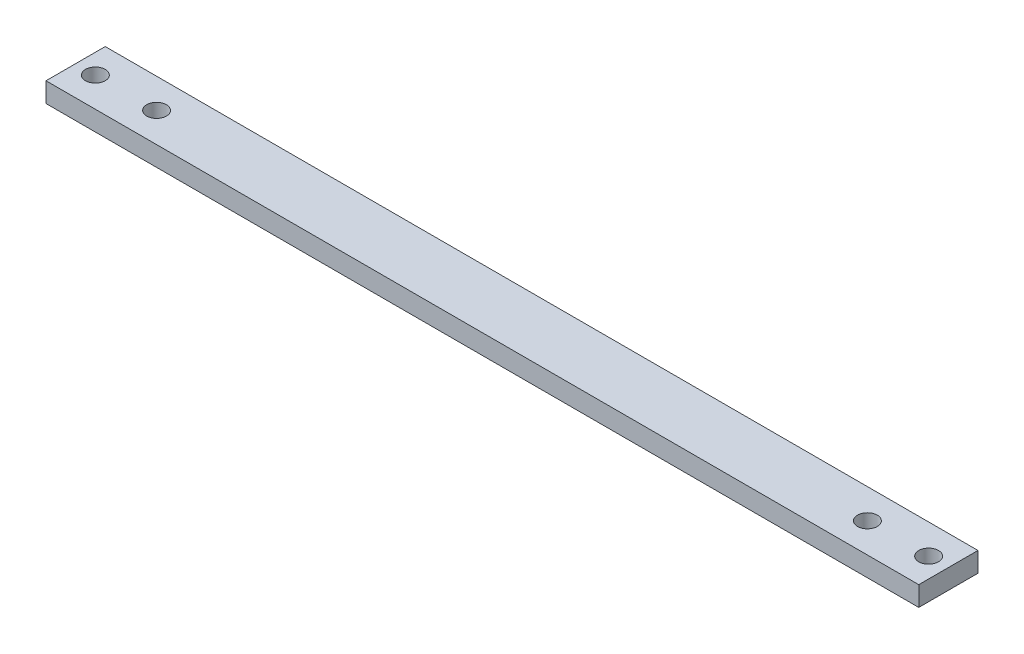
SolidWorks part; units mm, degrees
ref_plane "Front Plane" through (0, 0, 0) normal (0, 0, 1) x (1, 0, 0)
ref_plane "Top Plane" through (0, 0, 0) normal (0, 1, 0) x (1, 0, 0)
ref_plane "Right Plane" through (0, 0, 0) normal (1, 0, 0) x (0, 0, -1)
sketch "Sketch1" plane through (0, 0, 0) normal (0, 1, 0) x (1, 0, 0)
  line L0 (0, 7.5) -> (0, -7.5) construction
  line L1 (-110.5, 7.5) -> (110.5, 7.5)
  line L2 (-110.5, 7.5) -> (-110.5, -7.5)
  line L3 (-110.5, -7.5) -> (110.5, -7.5)
  line L4 (110.5, 7.5) -> (110.5, -7.5)
  line L5 (-110.5, 7.5) -> (110.5, -7.5) construction
  line L6 (-110.5, -7.5) -> (110.5, 7.5) construction
  circle A0 centre (105.5, 0) radius 2.5
  circle A1 centre (90, 0) radius 2.5
  circle A2 centre (-105.5, 0) radius 2.5
  circle A3 centre (-90, 0) radius 2.5
  point P0 (0, 0)
  dimension "D2" = 5
  dimension "D3" = 15.5
  dimension "D5" = 2.5
  dimension "D1" = 15
  dimension "D4" = 90
extrude "Boss-Extrude1" add sketch "Sketch1" along normal blind 5
